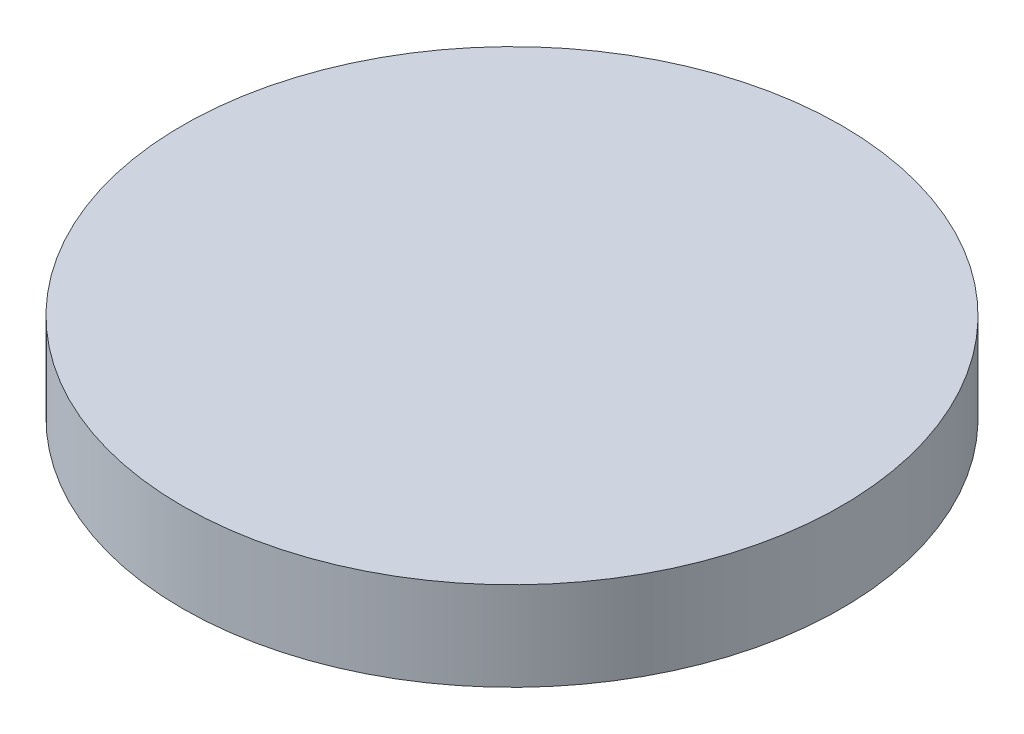
SolidWorks part; units mm, degrees
material "Alloy Steel"
ref_plane "Front Plane" through (0, 0, 0) normal (0, 0, 1) x (1, 0, 0)
ref_plane "Top Plane" through (0, 0, 0) normal (0, 1, 0) x (1, 0, 0)
ref_plane "Right Plane" through (0, 0, 0) normal (1, 0, 0) x (0, 0, -1)
sketch "Sketch1" plane through (0, 0, 0) normal (0, 1, 0) x (1, 0, 0)
  circle A0 centre (0, 0) radius 12.25
  dimension "D1" = 24.5
extrude "Boss-Extrude1" add sketch "Sketch1" along normal blind 3.302
